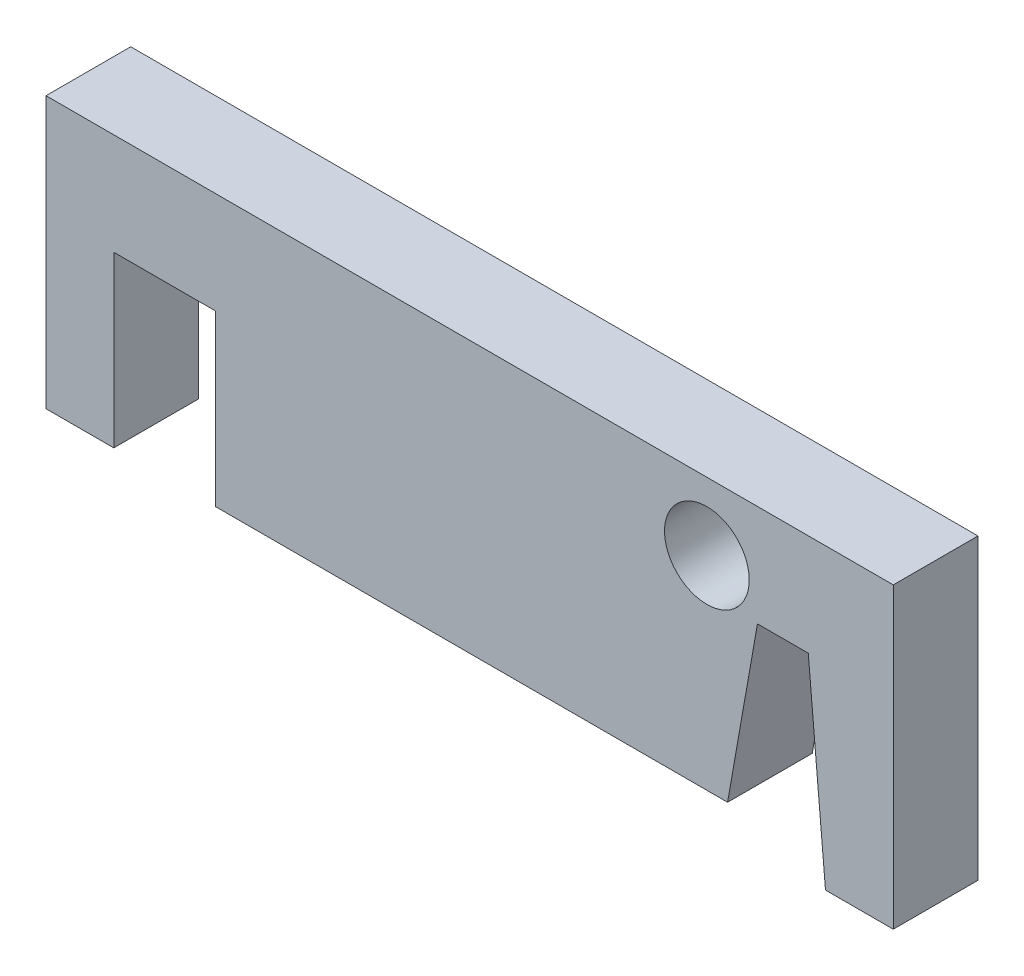
SolidWorks part; units mm, degrees
ref_plane "Front Plane" through (0, 0, 0) normal (0, 0, 1) x (1, 0, 0)
ref_plane "Top Plane" through (0, 0, 0) normal (0, 1, 0) x (1, 0, 0)
ref_plane "Right Plane" through (0, 0, 0) normal (1, 0, 0) x (0, 0, -1)
sketch "Sketch1" plane through (0, 0, 0) normal (0, 0, 1) x (1, 0, 0)
  line L0 (25.3811, -1.27) -> (26.67, -16.002)
  line L1 (-31.75, -6.35) -> (31.75, -6.35)
  line L2 (-31.75, -6.35) -> (-31.75, 6.35)
  line L3 (-31.75, 6.35) -> (31.75, 6.35)
  line L4 (31.75, -6.35) -> (31.75, 6.35)
  line L5 (-31.75, -6.35) -> (31.75, 6.35) construction
  line L6 (-31.75, 6.35) -> (31.75, -6.35) construction
  line L7 (0, 6.35) -> (-6.35, 6.35)
  line L11 (26.67, -16.002) -> (31.75, -16.002)
  line L12 (25.3811, -1.27) -> (21.5711, -1.27)
  line L13 (21.5711, -1.27) -> (19.3318, -13.97)
  line L14 (19.3318, -13.97) -> (-31.75, -13.97)
  line L15 (-31.75, -6.35) -> (-31.75, -13.97)
  line L16 (31.75, -6.35) -> (31.75, -16.002)
  circle A0 centre (17.78, 1.27) radius 3.175
  point P0 (0, 0)
  dimension "D6" = 6.35
  dimension "D1" = 63.5
  dimension "D2" = 12.7
  dimension "D3" = 7.62
  dimension "D7" = 49.53
  dimension "D8" = 5
  dimension "D9" = 5.08
  dimension "D10" = 14.732
  dimension "D11" = 100
  dimension "D12" = 3.81
  dimension "D13" = 12.7
  dimension "D14" = 15.24
extrude "Boss-Extrude1" add sketch "Sketch1" along normal mid plane 6.35
sketch "Sketch2" plane through (0, 0, 3.175) normal (0, 0, 1) x (1, 0, 0)
  line L0 (19.3318, -13.97) -> (-31.75, -13.97) construction
  line L1 (-19.05, -13.97) -> (-26.67, -13.97)
  line L2 (-19.05, -13.97) -> (-19.05, -1.27)
  line L3 (-19.05, -1.27) -> (-26.67, -1.27)
  line L4 (-26.67, -13.97) -> (-26.67, -1.27)
  line L5 (-31.75, -13.97) -> (-31.75, 6.35) construction
  dimension "D1" = 5.08
  dimension "D2" = 7.62
  dimension "D3" = 12.7
extrude "Cut-Extrude1" cut sketch "Sketch2" against normal through all
